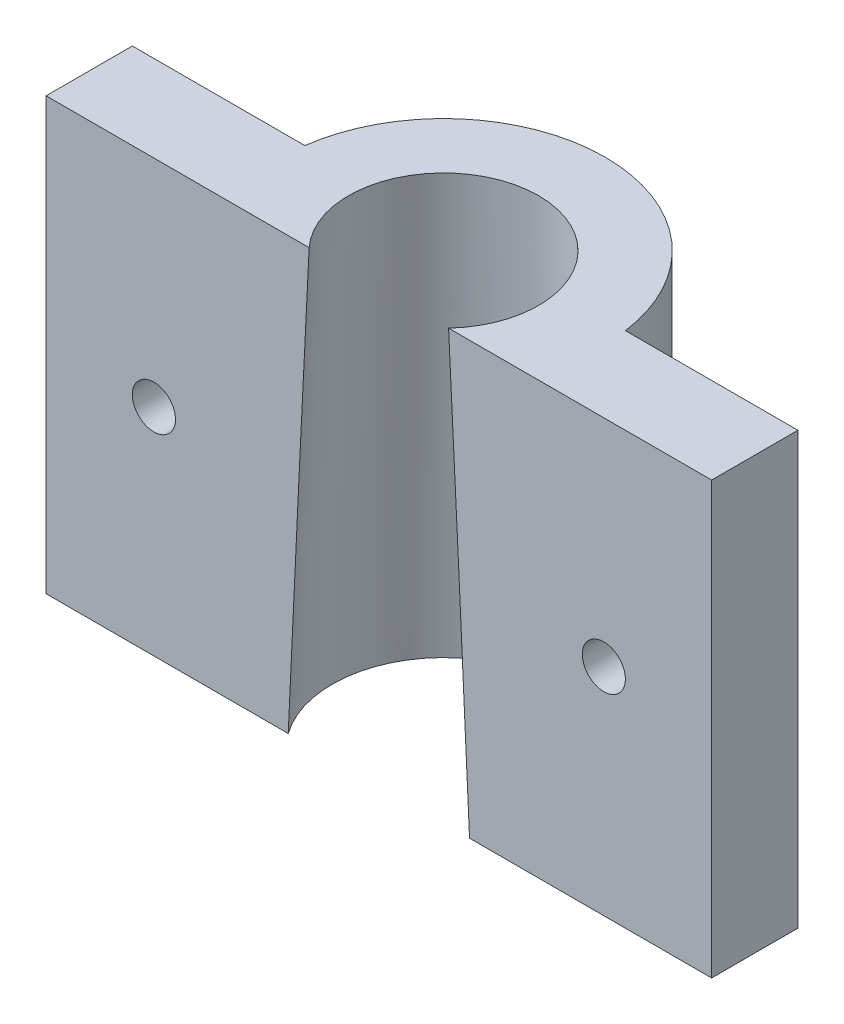
SolidWorks part; units mm, degrees
ref_plane "Plano frontal" through (0, 0, 0) normal (0, 0, 1) x (1, 0, 0)
ref_plane "Plano superior" through (0, 0, 0) normal (0, 1, 0) x (1, 0, 0)
ref_plane "Plano direito" through (0, 0, 0) normal (1, 0, 0) x (0, 0, -1)
sketch "Esboço4" plane through (0, 0, 0) normal (0, 1, 0) x (1, 0, 0)
  line L0 (-30.0565, 0) -> (38.5311, 0) construction
  line L1 (0, -30.791) -> (0, 22.4294) construction
  line L2 (15.433, -3) -> (-15.433, -3)
  line L9 (-15.433, -3) -> (-15.433, 1)
  line L10 (-15.433, 1) -> (-7.433, 1)
  line L11 (15.433, -3) -> (15.433, 1)
  line L12 (15.433, 1) -> (7.433, 1)
  arc A0 (7.433, 1) -> (-7.433, 1) centre (0, 0) ccw
  point P12 (0, 0)
  point P18 (0, -3)
  dimension "D7" = 15
  dimension "D4" = 3
  dimension "D5" = 8
  dimension "D6" = 4
extrude "Ressalto-extrusão3" add sketch "Esboço4" along normal blind 60
sketch "Esboço5" plane through (0, 0, 0) normal (0, 1, 0) x (1, 0, 0)
  circle A0 centre (0, 0) radius 6
  dimension "D1" = 12
extrude "Corte-extrusão1" cut sketch "Esboço5" along normal blind 17
sketch "Esboço6" plane through (0, 0, 0) normal (0, 0, 1) x (1, 0, 0)
  line L0 (0, -9.9431) -> (0, 70.6323) construction
  line L1 (0, 17) -> (-5.75, 17)
  line L3 (0, 70) -> (-3.75, 70)
  line L5 (-6, 17) -> (6, 17) construction
  line L6 (-3.75, 70) -> (-5.75, 17)
  line L7 (0, 70) -> (0, 17)
  dimension "D1" = 3.75
  dimension "D2" = 5.75
  dimension "D3" = 53
revolve "Corte-Revolução1" cut sketch "Esboço6" angle 360 about L7
sketch "Esboço7" plane through (0, 0, 3) normal (0, 0, 1) x (1, 0, 0)
  line L0 (15.433, 60) -> (15.433, 0) construction
  line L1 (-15.433, 0) -> (15.433, 0)
  line L2 (-15.433, 0) -> (-15.433, 32.5)
  line L3 (-15.433, 32.5) -> (15.433, 32.5)
  line L4 (15.433, 0) -> (15.433, 32.5)
  line L6 (-15.433, 60) -> (15.433, 60)
  line L7 (-15.433, 60) -> (-15.433, 52.5)
  line L8 (-15.433, 52.5) -> (15.433, 52.5)
  line L9 (15.433, 60) -> (15.433, 52.5)
  dimension "D1" = 32.5
  dimension "D2" = 7.5
extrude "Corte-extrusão2" cut sketch "Esboço7" against normal blind 15
sketch "Esboço8" plane through (0, 0, -1) normal (0, 0, -1) x (-1, 0, 0)
  line L0 (0, 60.9512) -> (0, 18.1481) construction
  line L1 (-22.3614, 42.5) -> (25.7766, 42.5) construction
  line L2 (-10.433, 55.2733) -> (-10.433, 29.1674) construction
  circle A0 centre (-10.433, 42.5) radius 1
  circle A1 centre (10.433, 42.5) radius 1
  dimension "D1" = 2
extrude "Corte-extrusão3" cut sketch "Esboço8" against normal through all
